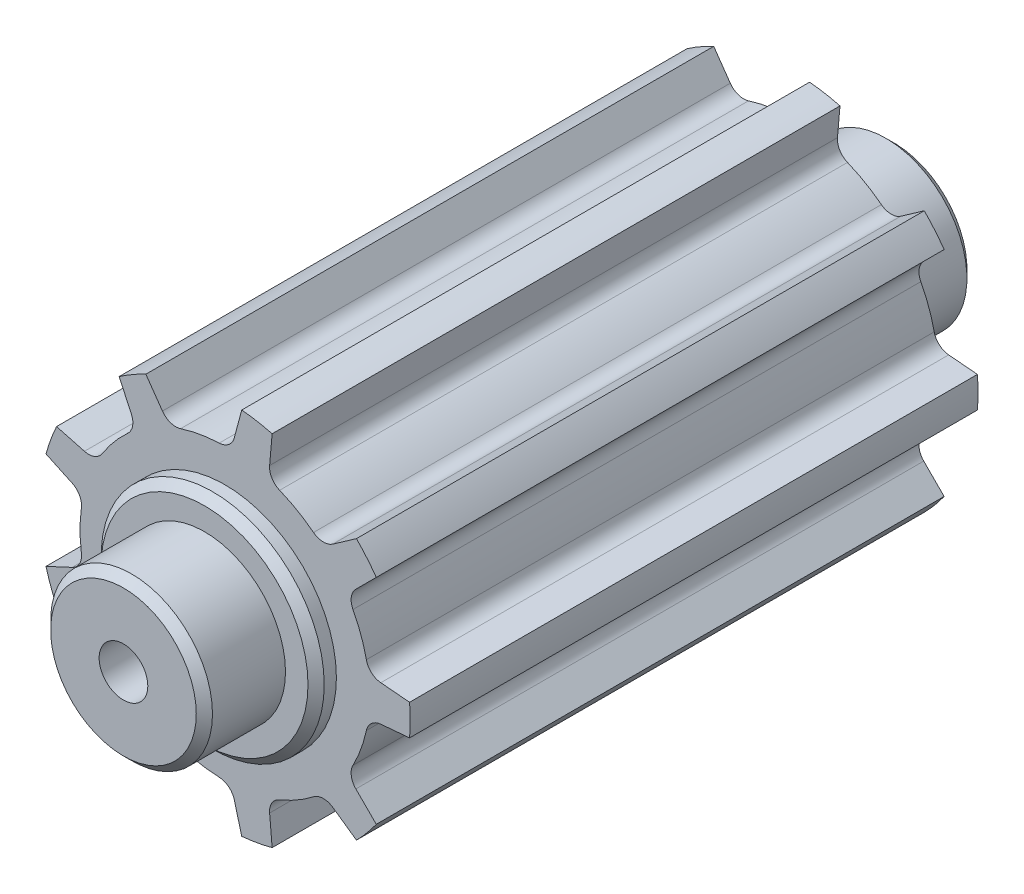
SolidWorks part; units mm, degrees
ref_plane "Front Plane" through (0, 0, 0) normal (0, 0, 1) x (1, 0, 0)
ref_plane "Top Plane" through (0, 0, 0) normal (0, 1, 0) x (1, 0, 0)
ref_plane "Right Plane" through (0, 0, 0) normal (1, 0, 0) x (0, 0, -1)
sketch "Sketch2" plane through (0, 0, 0) normal (0, 0, 1) x (1, 0, 0)
  line L0 (0, 0) -> (-7.1505, 0) construction
  line L1 (-4.4096, -1.2) -> (-3.7645, -0.8992)
  line L2 (-4.4096, 1.2) -> (-3.7645, 0.8992)
  line L3 (-2.6066, 3.7537) -> (-2.3058, 3.1086)
  line L4 (-4.1493, 1.9152) -> (-3.4618, 1.731)
  line L5 (0.416, 4.551) -> (0.2318, 3.8635)
  line L6 (-1.9475, 4.1343) -> (-1.5392, 3.5512)
  line L7 (3.244, 3.2189) -> (2.661, 2.8106)
  line L8 (1.1656, 4.4189) -> (1.1035, 3.7098)
  line L9 (4.5541, 0.3806) -> (3.845, 0.4426)
  line L10 (3.7333, 2.6358) -> (3.23, 2.1325)
  line L11 (3.7333, -2.6358) -> (3.23, -2.1325)
  line L12 (4.5541, -0.3806) -> (3.845, -0.4426)
  line L13 (1.1656, -4.4189) -> (1.1035, -3.7098)
  line L14 (3.244, -3.2189) -> (2.661, -2.8106)
  line L15 (-1.9475, -4.1343) -> (-1.5392, -3.5512)
  line L16 (0.416, -4.551) -> (0.2318, -3.8635)
  line L17 (-4.1493, -1.9152) -> (-3.4618, -1.731)
  line L18 (-2.6066, -3.7537) -> (-2.3058, -3.1086)
  arc A0 (-3.5372, 0.4826) -> (-3.5372, -0.4826) centre (0, 0) ccw
  arc A1 (-4.1493, 1.9152) -> (-4.4096, 1.2) centre (0, 0) ccw construction
  arc A2 (-3.7645, -0.8992) -> (-3.5372, -0.4826) centre (-3.9336, -0.5367) ccw
  arc A3 (-3.7645, 0.8992) -> (-3.5372, 0.4826) centre (-3.9336, 0.5367) cw
  arc A4 (-4.1493, 1.9152) -> (-4.4096, 1.2) centre (0, 0) ccw construction
  arc A5 (-2.3058, 3.1086) -> (-2.3995, 2.6434) centre (-2.6683, 2.9395) cw
  arc A6 (-2.3995, 2.6434) -> (-3.0199, 1.904) centre (0, 0) ccw
  arc A7 (-3.4618, 1.731) -> (-3.0199, 1.904) centre (-3.3582, 2.1173) ccw
  arc A8 (-4.1493, 1.9152) -> (-4.4096, 1.2) centre (0, 0) ccw construction
  arc A9 (0.2318, 3.8635) -> (-0.139, 3.5673) centre (-0.1546, 3.967) cw
  arc A10 (-0.139, 3.5673) -> (-1.0895, 3.3997) centre (0, 0) ccw
  arc A11 (-1.5392, 3.5512) -> (-1.0895, 3.3997) centre (-1.2116, 3.7806) ccw
  arc A12 (-4.1493, 1.9152) -> (-4.4096, 1.2) centre (0, 0) ccw
  arc A13 (2.661, 2.8106) -> (2.1865, 2.822) centre (2.4315, 3.1382) cw
  arc A14 (2.1865, 2.822) -> (1.3507, 3.3046) centre (0, 0) ccw
  arc A15 (1.1035, 3.7098) -> (1.3507, 3.3046) centre (1.502, 3.6749) ccw
  arc A16 (-4.1493, 1.9152) -> (-4.4096, 1.2) centre (0, 0) ccw
  arc A17 (3.845, 0.4426) -> (3.489, 0.7563) centre (3.8799, 0.8411) cw
  arc A18 (3.489, 0.7563) -> (3.1589, 1.6633) centre (0, 0) ccw
  arc A19 (3.23, 2.1325) -> (3.1589, 1.6633) centre (3.5128, 1.8496) ccw
  arc A20 (-4.1493, 1.9152) -> (-4.4096, 1.2) centre (0, 0) ccw
  arc A21 (3.23, -2.1325) -> (3.1589, -1.6633) centre (3.5128, -1.8496) cw
  arc A22 (3.1589, -1.6633) -> (3.489, -0.7563) centre (0, 0) ccw
  arc A23 (3.845, -0.4426) -> (3.489, -0.7563) centre (3.8799, -0.8411) ccw
  arc A24 (-4.1493, 1.9152) -> (-4.4096, 1.2) centre (0, 0) ccw
  arc A25 (1.1035, -3.7098) -> (1.3507, -3.3046) centre (1.502, -3.6749) cw
  arc A26 (1.3507, -3.3046) -> (2.1865, -2.822) centre (0, 0) ccw
  arc A27 (2.661, -2.8106) -> (2.1865, -2.822) centre (2.4315, -3.1382) ccw
  arc A28 (-4.1493, 1.9152) -> (-4.4096, 1.2) centre (0, 0) ccw
  arc A29 (-1.5392, -3.5512) -> (-1.0895, -3.3997) centre (-1.2116, -3.7806) cw
  arc A30 (-1.0895, -3.3997) -> (-0.139, -3.5673) centre (0, 0) ccw
  arc A31 (0.2318, -3.8635) -> (-0.139, -3.5673) centre (-0.1546, -3.967) ccw
  arc A32 (-4.1493, 1.9152) -> (-4.4096, 1.2) centre (0, 0) ccw
  arc A33 (-3.4618, -1.731) -> (-3.0199, -1.904) centre (-3.3582, -2.1173) cw
  arc A34 (-3.0199, -1.904) -> (-2.3995, -2.6434) centre (0, 0) ccw
  arc A35 (-2.3058, -3.1086) -> (-2.3995, -2.6434) centre (-2.6683, -2.9395) ccw
  circle A36 centre (0, 0) radius 2
  arc A37 (-1.9475, 4.1343) -> (-2.6066, 3.7537) centre (0, 0) ccw construction
  arc A38 (-1.9475, 4.1343) -> (-2.6066, 3.7537) centre (0, 0) ccw construction
  arc A39 (-1.9475, 4.1343) -> (-2.6066, 3.7537) centre (0, 0) ccw construction
  arc A40 (-1.9475, 4.1343) -> (-2.6066, 3.7537) centre (0, 0) ccw
  arc A41 (-1.9475, 4.1343) -> (-2.6066, 3.7537) centre (0, 0) ccw
  arc A42 (-1.9475, 4.1343) -> (-2.6066, 3.7537) centre (0, 0) ccw
  arc A43 (-1.9475, 4.1343) -> (-2.6066, 3.7537) centre (0, 0) ccw
  arc A44 (-1.9475, 4.1343) -> (-2.6066, 3.7537) centre (0, 0) ccw
  arc A45 (-1.9475, 4.1343) -> (-2.6066, 3.7537) centre (0, 0) ccw
  arc A46 (-2.6066, -3.7537) -> (-1.9475, -4.1343) centre (0, 0) ccw construction
  arc A47 (-2.6066, -3.7537) -> (-1.9475, -4.1343) centre (0, 0) ccw construction
  arc A48 (-2.6066, -3.7537) -> (-1.9475, -4.1343) centre (0, 0) ccw construction
  arc A49 (-2.6066, -3.7537) -> (-1.9475, -4.1343) centre (0, 0) ccw
  arc A50 (-2.6066, -3.7537) -> (-1.9475, -4.1343) centre (0, 0) ccw
  arc A51 (-2.6066, -3.7537) -> (-1.9475, -4.1343) centre (0, 0) ccw
  arc A52 (-2.6066, -3.7537) -> (-1.9475, -4.1343) centre (0, 0) ccw
  arc A53 (-2.6066, -3.7537) -> (-1.9475, -4.1343) centre (0, 0) ccw
  arc A54 (-2.6066, -3.7537) -> (-1.9475, -4.1343) centre (0, 0) ccw
  arc A55 (0.416, -4.551) -> (1.1656, -4.4189) centre (0, 0) ccw construction
  arc A56 (0.416, -4.551) -> (1.1656, -4.4189) centre (0, 0) ccw construction
  arc A57 (0.416, -4.551) -> (1.1656, -4.4189) centre (0, 0) ccw construction
  arc A58 (0.416, -4.551) -> (1.1656, -4.4189) centre (0, 0) ccw
  arc A59 (0.416, -4.551) -> (1.1656, -4.4189) centre (0, 0) ccw
  arc A60 (0.416, -4.551) -> (1.1656, -4.4189) centre (0, 0) ccw
  arc A61 (0.416, -4.551) -> (1.1656, -4.4189) centre (0, 0) ccw
  arc A62 (0.416, -4.551) -> (1.1656, -4.4189) centre (0, 0) ccw
  arc A63 (0.416, -4.551) -> (1.1656, -4.4189) centre (0, 0) ccw
  arc A64 (3.244, -3.2189) -> (3.7333, -2.6358) centre (0, 0) ccw construction
  arc A65 (3.244, -3.2189) -> (3.7333, -2.6358) centre (0, 0) ccw construction
  arc A66 (3.244, -3.2189) -> (3.7333, -2.6358) centre (0, 0) ccw construction
  arc A67 (3.244, -3.2189) -> (3.7333, -2.6358) centre (0, 0) ccw
  arc A68 (3.244, -3.2189) -> (3.7333, -2.6358) centre (0, 0) ccw
  arc A69 (3.244, -3.2189) -> (3.7333, -2.6358) centre (0, 0) ccw
  arc A70 (3.244, -3.2189) -> (3.7333, -2.6358) centre (0, 0) ccw
  arc A71 (3.244, -3.2189) -> (3.7333, -2.6358) centre (0, 0) ccw
  arc A72 (3.244, -3.2189) -> (3.7333, -2.6358) centre (0, 0) ccw
  arc A73 (4.5541, -0.3806) -> (4.5541, 0.3806) centre (0, 0) ccw construction
  arc A74 (4.5541, -0.3806) -> (4.5541, 0.3806) centre (0, 0) ccw construction
  arc A75 (4.5541, -0.3806) -> (4.5541, 0.3806) centre (0, 0) ccw construction
  arc A76 (4.5541, -0.3806) -> (4.5541, 0.3806) centre (0, 0) ccw
  arc A77 (4.5541, -0.3806) -> (4.5541, 0.3806) centre (0, 0) ccw
  arc A78 (4.5541, -0.3806) -> (4.5541, 0.3806) centre (0, 0) ccw
  arc A79 (4.5541, -0.3806) -> (4.5541, 0.3806) centre (0, 0) ccw
  arc A80 (4.5541, -0.3806) -> (4.5541, 0.3806) centre (0, 0) ccw
  arc A81 (4.5541, -0.3806) -> (4.5541, 0.3806) centre (0, 0) ccw
  arc A82 (3.7333, 2.6358) -> (3.244, 3.2189) centre (0, 0) ccw construction
  arc A83 (3.7333, 2.6358) -> (3.244, 3.2189) centre (0, 0) ccw construction
  arc A84 (3.7333, 2.6358) -> (3.244, 3.2189) centre (0, 0) ccw construction
  arc A85 (3.7333, 2.6358) -> (3.244, 3.2189) centre (0, 0) ccw
  arc A86 (3.7333, 2.6358) -> (3.244, 3.2189) centre (0, 0) ccw
  arc A87 (3.7333, 2.6358) -> (3.244, 3.2189) centre (0, 0) ccw
  arc A88 (3.7333, 2.6358) -> (3.244, 3.2189) centre (0, 0) ccw
  arc A89 (3.7333, 2.6358) -> (3.244, 3.2189) centre (0, 0) ccw
  arc A90 (3.7333, 2.6358) -> (3.244, 3.2189) centre (0, 0) ccw
  arc A91 (1.1656, 4.4189) -> (0.416, 4.551) centre (0, 0) ccw construction
  arc A92 (1.1656, 4.4189) -> (0.416, 4.551) centre (0, 0) ccw construction
  arc A93 (1.1656, 4.4189) -> (0.416, 4.551) centre (0, 0) ccw construction
  arc A94 (1.1656, 4.4189) -> (0.416, 4.551) centre (0, 0) ccw
  arc A95 (1.1656, 4.4189) -> (0.416, 4.551) centre (0, 0) ccw
  arc A96 (1.1656, 4.4189) -> (0.416, 4.551) centre (0, 0) ccw
  arc A97 (1.1656, 4.4189) -> (0.416, 4.551) centre (0, 0) ccw
  arc A98 (1.1656, 4.4189) -> (0.416, 4.551) centre (0, 0) ccw
  arc A99 (1.1656, 4.4189) -> (0.416, 4.551) centre (0, 0) ccw
  arc A100 (-4.4096, -1.2) -> (-4.1493, -1.9152) centre (0, 0) ccw construction
  arc A101 (-4.4096, -1.2) -> (-4.1493, -1.9152) centre (0, 0) ccw construction
  arc A102 (-4.4096, -1.2) -> (-4.1493, -1.9152) centre (0, 0) ccw construction
  arc A103 (-4.4096, -1.2) -> (-4.1493, -1.9152) centre (0, 0) ccw
  arc A104 (-4.4096, -1.2) -> (-4.1493, -1.9152) centre (0, 0) ccw
  arc A105 (-4.4096, -1.2) -> (-4.1493, -1.9152) centre (0, 0) ccw
  arc A106 (-4.4096, -1.2) -> (-4.1493, -1.9152) centre (0, 0) ccw
  arc A107 (-4.4096, -1.2) -> (-4.1493, -1.9152) centre (0, 0) ccw
  arc A108 (-4.4096, -1.2) -> (-4.1493, -1.9152) centre (0, 0) ccw
  point P86 (0, 0)
  dimension "D1" = 7.14
  dimension "D2" = 9.14
  dimension "D5" = 0.4
  dimension "D7" = 4
  dimension "D3" = 25
  dimension "D4" = 1.2
  dimension "D6" = 9
extrude "Boss-Extrude1" add sketch "Sketch2" along normal blind 14 contours L1 A103 L17 A33 A34 A35 L18 A49 L15 A29 A30 A31 L16 A58 L13 A25 A26 A27 L14 A67 L11 A21 A22 A23 L12 A76 L9 A17 A18 A19 L10 A85 L7 A13 A14 A15 L8 A94 L5 A9 A10 A11 L6 A40 L3 A5 A6 A7 L4 A12 L2
sketch "Sketch3" plane through (0, 0, 14) normal (0, 0, 1) x (1, 0, 0)
  circle A0 centre (0, 0) radius 2.75
  dimension "D1" = 5.5
extrude "Boss-Extrude2" add sketch "Sketch3" against normal blind 14.5
sketch "Sketch4" plane through (0, 0, 14) normal (0, 0, 1) x (1, 0, 0)
  circle A0 centre (0, 0) radius 2.75
  dimension "D1" = 5.5
extrude "Boss-Extrude3" add sketch "Sketch4" along normal blind 0.5
sketch "Sketch5" plane through (0, 0, 14.5) normal (0, 0, 1) x (1, 0, 0)
  circle A0 centre (0, 0) radius 1.995
  dimension "D1" = 3.99
extrude "Boss-Extrude4" add sketch "Sketch5" along normal blind 2
sketch "Sketch6" plane through (0, 0, -0.5) normal (0, 0, -1) x (-1, 0, 0)
  circle A0 centre (0, 0) radius 1.995
  dimension "D1" = 3.99
extrude "Boss-Extrude5" add sketch "Sketch6" along normal blind 2
sketch "Sketch7" plane through (0, 0, -2.5) normal (0, 0, -1) x (-1, 0, 0)
  circle A0 centre (0, 0) radius 0.6
  dimension "D1" = 1.2
extrude "Cut-Extrude1" cut sketch "Sketch7" against normal blind 21
chamfer "Chamfer1" distance 0.2 angle 45 4 edges at (1.995, 0, 16.5) (2.75, 0, 14.5) (2.75, 0, -0.5) (-1.995, 0, -2.5)
